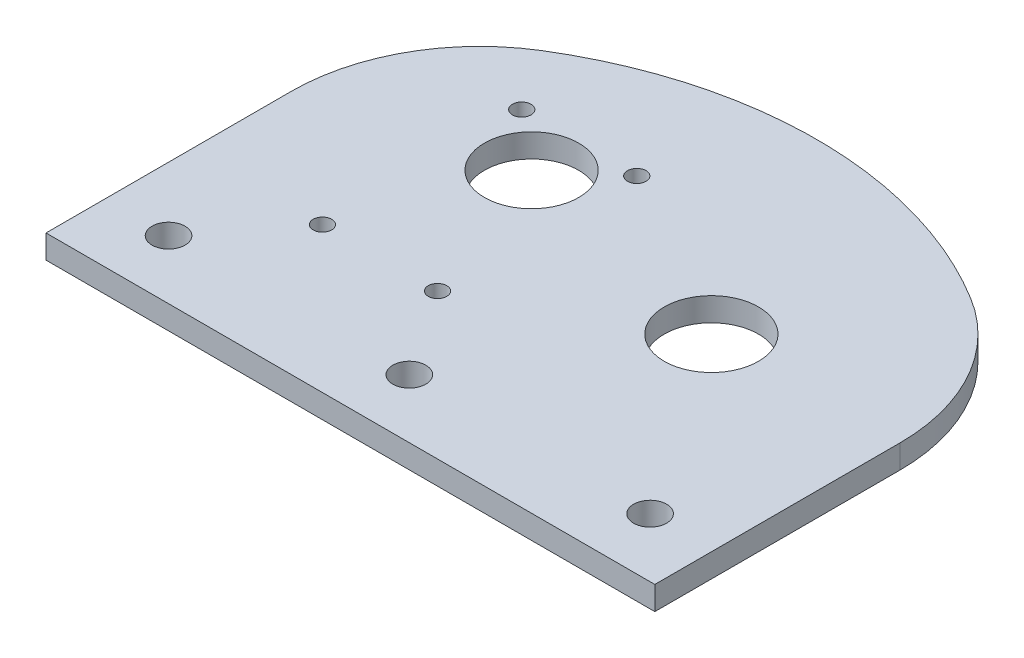
SolidWorks part; units mm, degrees
material "6061-T6 (SS)"
ref_plane "Front Plane" through (0, 0, 0) normal (0, 0, 1) x (1, 0, 0)
ref_plane "Top Plane" through (0, 0, 0) normal (0, 1, 0) x (1, 0, 0)
ref_plane "Right Plane" through (0, 0, 0) normal (1, 0, 0) x (0, 0, -1)
sketch "Sketch3" plane through (0, 0, 0) normal (0, 1, 0) x (1, 0, 0)
  line L0 (-25.4, 0) -> (-25.4, -25.4)
  line L1 (-25.4, -25.4) -> (0, -25.4)
  line L2 (0, -25.4) -> (25.4, -25.4)
  line L3 (25.4, -25.4) -> (25.4, 0)
  arc A0 (25.4, 0) -> (-25.4, 0) centre (0, 0) ccw
  circle A1 centre (0, 7) radius 6.35
  circle A2 centre (7.75, 13.4234) radius 1.25
  circle A3 centre (-7.75, 13.4234) radius 1.25
  circle A4 centre (-7.75, -13.4234) radius 1.25
  circle A5 centre (7.75, 13.4234) radius 1.25 construction
  circle A7 centre (-7.75, 13.4234) radius 1.25 construction
  circle A8 centre (-7.75, -13.4234) radius 1.25 construction
  circle A9 centre (7.75, -13.4234) radius 1.25 construction
  circle A10 centre (0, 7) radius 6 construction
  circle A14 centre (7.75, -13.4234) radius 1.25
  dimension "D1" = 12.7
  dimension "D2" = 25.4
extrude "Boss-Extrude4" add sketch "Sketch3" along normal mid plane 3.175
sketch "Sketch5" plane through (0, -1.5875, 0) normal (0, -1, 0) x (-1, 0, 0)
  line L0 (-25.4, 0) -> (-31.75, 0)
  line L1 (-25.4, -25.4) -> (-25.4, 0) construction
  line L2 (-82.55, -25.4) -> (-82.55, 0)
  line L3 (-82.55, -25.4) -> (-25.4, -25.4)
  line L4 (-25.4, 0) -> (-25.4, -25.4)
  arc A0 (25.4, 0) -> (-25.4, 0) centre (0, 0) ccw construction
  arc A1 (-82.55, 0) -> (-31.75, 0) centre (-57.15, 0) cw
  dimension "D1" = 6.35
extrude "Boss-Extrude5" [suppressed] add sketch "Sketch5" against normal blind 9.525 contours A1 L0 L4 L3 L2
sketch "Sketch8" plane through (0, 0, 0) normal (0, 1, 0) x (1, 0, 0)
  line L0 (0, 7) -> (31.225, 0) construction
  line L1 (25.4, -25.4) -> (25.4, 0) construction
  line L2 (25.4, -25.4) -> (25.4, 0)
  line L3 (25.4, -25.4) -> (56.625, -25.4)
  line L4 (56.625, -25.4) -> (56.625, 0)
  line L5 (-25.4, -25.4) -> (25.4, -25.4) construction
  arc A0 (-13.3008, 21.6391) -> (44.5258, 21.6391) centre (15.6125, -25.4) cw
  arc A1 (25.4, 0) -> (-25.4, 0) centre (0, 0) ccw construction
  arc A3 (25.4, 0) -> (-13.3008, 21.6391) centre (0, 0) ccw
  arc A4 (56.625, 0) -> (44.5258, 21.6391) centre (31.225, 0) ccw
  dimension "D1" = 32
extrude "Boss-Extrude7" add sketch "Sketch8" along normal through all and the other way through all
sketch "Sketch7" [suppressed] plane through (0, -4.7625, 0) normal (0, -1, 0) x (1, 0, 0)
  line L0 (-25.4, 25.4) -> (82.55, 25.4) construction
  line L1 (25.4, 0) -> (31.75, 0) construction
  line L2 (25.4, 0) -> (31.75, 0)
  arc A0 (76.1342, -16.8748) -> (-18.9842, -16.8748) centre (28.575, 25.4) cw
  arc A1 (31.75, 0) -> (82.55, 0) centre (57.15, 0) ccw construction
  arc A2 (-25.4, 0) -> (25.4, 0) centre (0, 0) ccw construction
  arc A3 (-18.9842, -16.8748) -> (25.4, 0) centre (0, 0) ccw
  arc A4 (31.75, 0) -> (76.1342, -16.8748) centre (57.15, 0) ccw
extrude "Boss-Extrude6" [suppressed] add sketch "Sketch7" against normal through all
sketch "Sketch6" [suppressed] plane through (0, -4.7625, 0) normal (0, -1, 0) x (-1, 0, 0)
  line L0 (-57.15, 0) -> (-31.47, 27.1359) construction
  line L1 (-31.47, 27.1359) -> (0, 7) construction
  line L2 (-31.47, 27.1359) -> (-30.312, 17.6815) construction
  line L3 (-28.3186, 27.5219) -> (-27.1606, 18.0675)
  line L4 (-34.6215, 26.7499) -> (-33.4635, 17.2955)
  line L5 (-57.15, 0) -> (-30.312, 17.6815) construction
  line L6 (-30.312, 17.6815) -> (0, 7) construction
  line L7 (-59.466, 18.9087) -> (-2.316, 25.9087) construction
  circle A0 centre (-57.15, 0) radius 6.35
  arc A1 (-28.3186, 27.5219) -> (-34.6215, 26.7499) centre (-31.47, 27.1359) ccw
  arc A2 (-76.1342, 16.8748) -> (-82.55, 0) centre (-57.15, 0) ccw construction
  arc A3 (-33.4635, 17.2955) -> (-27.1606, 18.0675) centre (-30.312, 17.6815) ccw
  circle A4 centre (-31.47, 27.1359) radius 4.7625 construction
  circle A5 centre (-57.15, 0) radius 19.05 construction
  circle A6 centre (0, 7) radius 19.05 construction
  point P6 (-30.891, 22.4087)
  dimension "D1" = 12.7
  dimension "D2" = 9.525
  dimension "D3" = 6.35
  dimension "D4" = 9.525
  dimension "D5" = 38.1
extrude "Cut-Extrude2" [suppressed] cut sketch "Sketch6" against normal blind 9.525 contours A0
sketch "Sketch9" plane through (0, 1.5875, 0) normal (0, 1, 0) x (1, 0, 0)
  circle A0 centre (31.225, 0) radius 6.35
  dimension "D1" = 12.7
extrude "Cut-Extrude3" cut sketch "Sketch9" against normal through all
sketch "Sketch11" plane through (0, 0, 25.4) normal (0, 0, 1) x (1, 0, 0)
  line L0 (-25.4, -1.5875) -> (56.625, -1.5875) construction
  line L1 (56.625, 1.5875) -> (-25.4, 1.5875)
  line L2 (56.625, 1.5875) -> (56.625, -1.5875)
  line L3 (56.625, -1.5875) -> (-25.4, -1.5875)
  line L4 (-25.4, 1.5875) -> (-25.4, -1.5875)
  line L5 (56.625, 1.5875) -> (-25.4, -1.5875) construction
  line L6 (56.625, -1.5875) -> (-25.4, 1.5875) construction
  line L7 (-25.4, 1.5875) -> (-25.4, -1.5875) construction
  line L8 (-25.4, 1.5875) -> (56.625, 1.5875) construction
  point P0 (15.6125, 0)
extrude "Boss-Extrude8" add sketch "Sketch11" along normal blind 7.62
sketch "Sketch10" plane through (0, -1.5875, 0) normal (0, -1, 0) x (-1, 0, 0)
  line L0 (-48.0525, -25.0825) -> (-15.6125, -25.0825) construction
  line L1 (-15.6125, -25.0825) -> (16.8275, -25.0825) construction
  line L2 (-56.625, -33.02) -> (-56.625, 0) construction
  line L4 (25.654, -17.145) -> (25.654, -33.02) construction
  line L5 (25.4, -33.02) -> (-56.625, -33.02) construction
  circle A0 centre (-15.6125, -25.0825) radius 2.2225
  circle A1 centre (-48.0525, -25.0825) radius 2.2225
  circle A2 centre (16.8275, -25.0825) radius 2.2225
  point P6 (-50.275, -25.0825)
  point P12 (-48.0525, -27.305)
  point P15 (25.654, -25.0825)
  point P16 (-15.6125, -33.02)
  dimension "D1" = 4.445
  dimension "D2" = 6.35
extrude "Cut-Extrude4" cut sketch "Sketch10" against normal through all contours A1
equation "\".25n\"=0.5"
